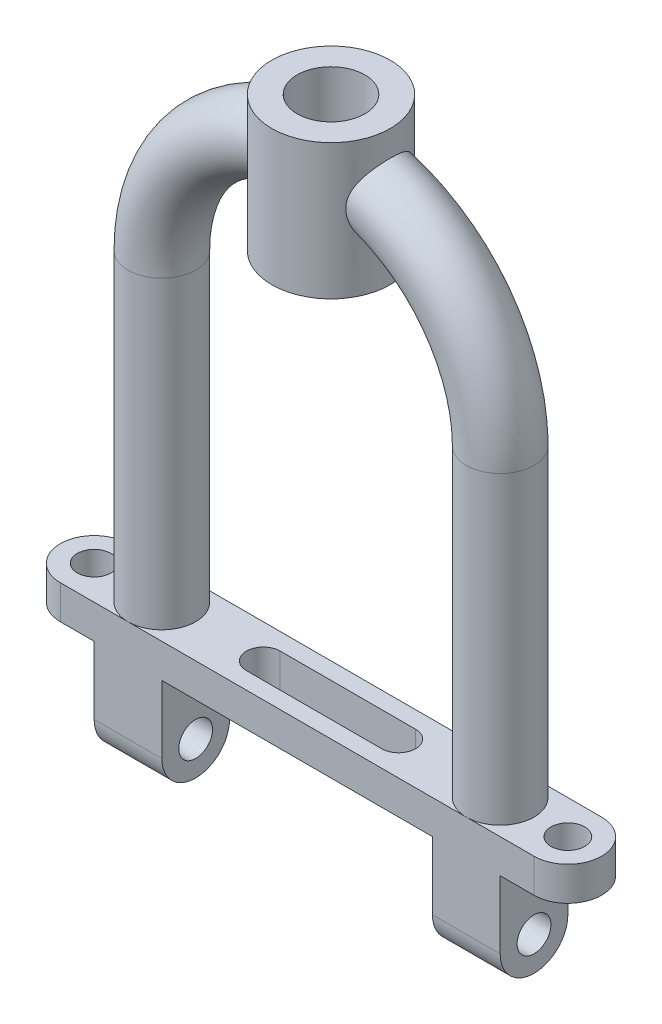
SolidWorks part; units mm, degrees
ref_plane "Plano frontal" through (0, 0, 0) normal (0, 0, 1) x (1, 0, 0)
ref_plane "Plano superior" through (0, 0, 0) normal (0, 1, 0) x (1, 0, 0)
ref_plane "Plano direito" through (0, 0, 0) normal (1, 0, 0) x (0, 0, -1)
sketch "Esboço1" plane through (0, 0, 0) normal (0, 1, 0) x (1, 0, 0)
  line L0 (-3.5, 0) -> (3.5, 0) construction
  line L1 (-3.5, 0.5) -> (3.5, 0.5)
  line L2 (-3.5, -0.5) -> (3.5, -0.5)
  line L3 (-1, 0) -> (1, 0) construction
  line L4 (-1, 0.25) -> (1, 0.25)
  line L5 (-1, -0.25) -> (1, -0.25)
  arc A0 (-3.5, 0.5) -> (-3.5, -0.5) centre (-3.5, 0) ccw
  arc A1 (3.5, -0.5) -> (3.5, 0.5) centre (3.5, 0) ccw
  circle A2 centre (3.5, 0) radius 0.25
  circle A3 centre (-3.5, 0) radius 0.25
  arc A4 (-1, 0.25) -> (-1, -0.25) centre (-1, 0) ccw
  arc A5 (1, -0.25) -> (1, 0.25) centre (1, 0) ccw
  point P2 (0, 0)
  point P14 (0, 0)
  dimension "D3" = 0.5
  dimension "D1" = 3.5
  dimension "D2" = 0.5
  dimension "D4" = 2
extrude "Ressalto-extrusão1" add sketch "Esboço1" along normal mid plane 0.5
sketch "Esboço2" plane through (0, 0.25, 0) normal (0, 1, 0) x (1, 0, 0)
  line L0 (-1, 0) -> (-2.5, 0) construction
  circle A1 centre (-2.5, 0) radius 0.5
sketch "Esboço3" plane through (0, 0, 0) normal (0, 0, 1) x (1, 0, 0)
  line L0 (-2.5, 0.25) -> (-2.5, 4.75)
  line L1 (-2, 0.25) -> (-3, 0.25) construction
  line L2 (-2.5, 4.75) -> (0, 4.75) construction
  line L3 (2.5, 4.75) -> (2.5, 0.25)
  line L4 (3.5, 0.25) -> (-3.5, 0.25) construction
  arc A0 (-2.5, 4.75) -> (2.5, 4.75) centre (0, 4.75) cw
  dimension "D1" = 4.5
  dimension "D2" = 2.5
sweep "Varredura1" add profiles "Esboço2" path "Esboço3"
ref_plane "Plano1" through (-2.5, 0, 0) normal (1, 0, 0) x (0, 0, -1)
sketch "Esboço5" plane through (-2.5, 0, 0) normal (1, 0, 0) x (0, 0, -1)
  line L0 (0.5, -0.25) -> (-0.5, -0.25)
  line L1 (0.5, -0.25) -> (0.5, -1.25)
  line L2 (-0.5, -0.25) -> (-0.5, -1.25)
  arc A0 (-0.5, -1.25) -> (0.5, -1.25) centre (0, -1.25) ccw
  circle A1 centre (0, -1.25) radius 0.25
  dimension "D1" = 1
extrude "Ressalto-extrusão2" add sketch "Esboço5" along normal mid plane 1
mirror "Espelhar1" about plane through (0, 0, 0) normal (1, 0, 0) of "Ressalto-extrusão2"
ref_plane "Plano2" through (0, 6, 0) normal (0, 1, 0) x (1, 0, 0)
sketch "Esboço6" plane through (0, 6, 0) normal (0, 1, 0) x (1, 0, 0)
  circle A0 centre (0, 0) radius 0.875
extrude "Ressalto-extrusão3" add sketch "Esboço6" along normal blind 2
ref_plane "Plano4" through (0, 8, 0) normal (0, 1, 0) x (1, 0, 0)
sketch "Esboço7" plane through (0, 8, 0) normal (0, 1, 0) x (1, 0, 0)
  circle A0 centre (0, 0) radius 0.5
extrude "Corte-extrusão1" cut sketch "Esboço7" against normal blind 2
